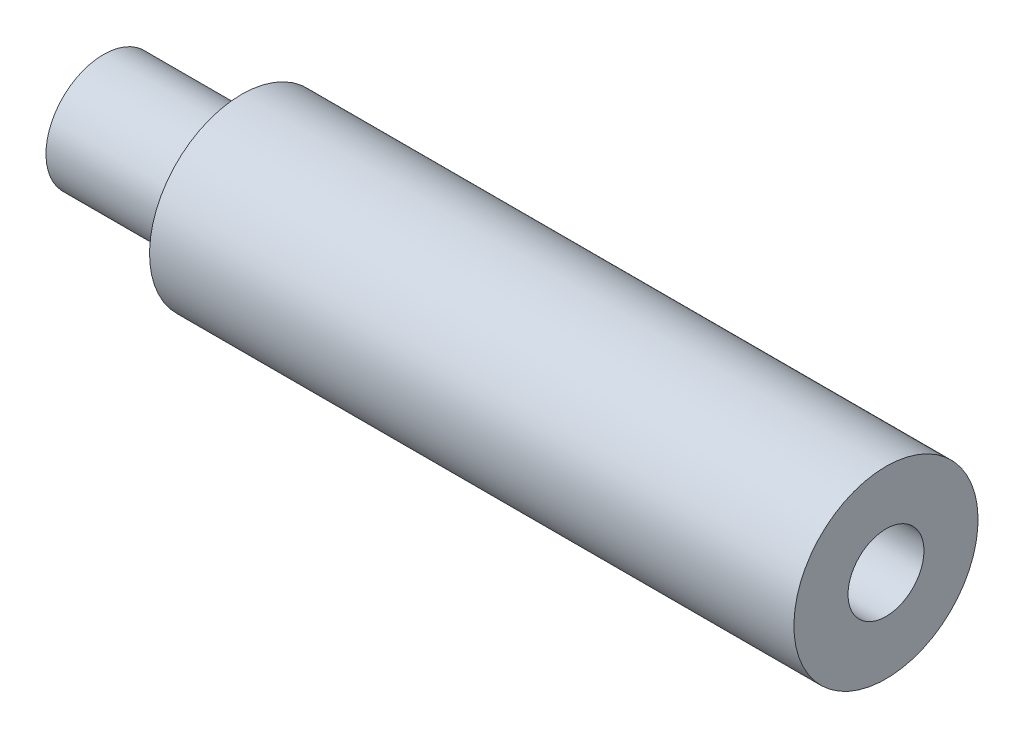
SolidWorks part; units mm, degrees
material "Alliage 7079"
ref_plane "Face" through (0, 0, 0) normal (0, 0, 1) x (1, 0, 0)
ref_plane "Dessus" through (0, 0, 0) normal (0, 1, 0) x (1, 0, 0)
ref_plane "Droite" through (0, 0, 0) normal (1, 0, 0) x (0, 0, -1)
sketch "Esquisse1" plane through (0, 0, 0) normal (0, 0, 1) x (1, 0, 0)
  line L0 (0, 0) -> (0, 2.5)
  line L1 (0, 2.5) -> (6, 2.5)
  line L2 (6, 2.5) -> (6, 4)
  line L3 (6, 4) -> (34, 4)
  line L4 (34, 4) -> (34, 0)
  line L5 (34, 0) -> (0, 0)
  dimension "D1" = 2.5
  dimension "D2" = 4
  dimension "D3" = 34
  dimension "D4" = 28
revolve "Révolution1" add sketch "Esquisse1" angle 360 about L5
hole_wizard "Trou taraudé M41" positions "Esquisse3" profile "Esquisse2" tap size "M4" standard "ISO"
sketch "Esquisse3" plane through (34, -0.2826, -1.4257) normal (-1, 0, 0) x (0, 0, 1)
  point P0 (1.4257, 0.2826)
sketch "Esquisse2" plane through (34, 0, 0) normal (0, 1, 0) x (0, 0, -1)
  line L0 (0, 0) -> (0, 25.9914)
  line L1 (0, 25.9914) -> (1.65, 25)
  line L2 (1.65, 25) -> (1.65, 0)
  line L5 (1.65, 0) -> (0, 0)
  line L10 (0, 25.9914) -> (-1.65, 25) construction
  line L11 (0, -6.35) -> (0, 107.95) construction
  dimension "Diamètre du trou pour taraudage" = 3.3
  dimension "Profondeur du trou pour taraudage" = 25
  dimension "Angle de pointe" = 118
cosmetic thread "Filetage de perçage1" parameters "D1"=10, "D2"=4
